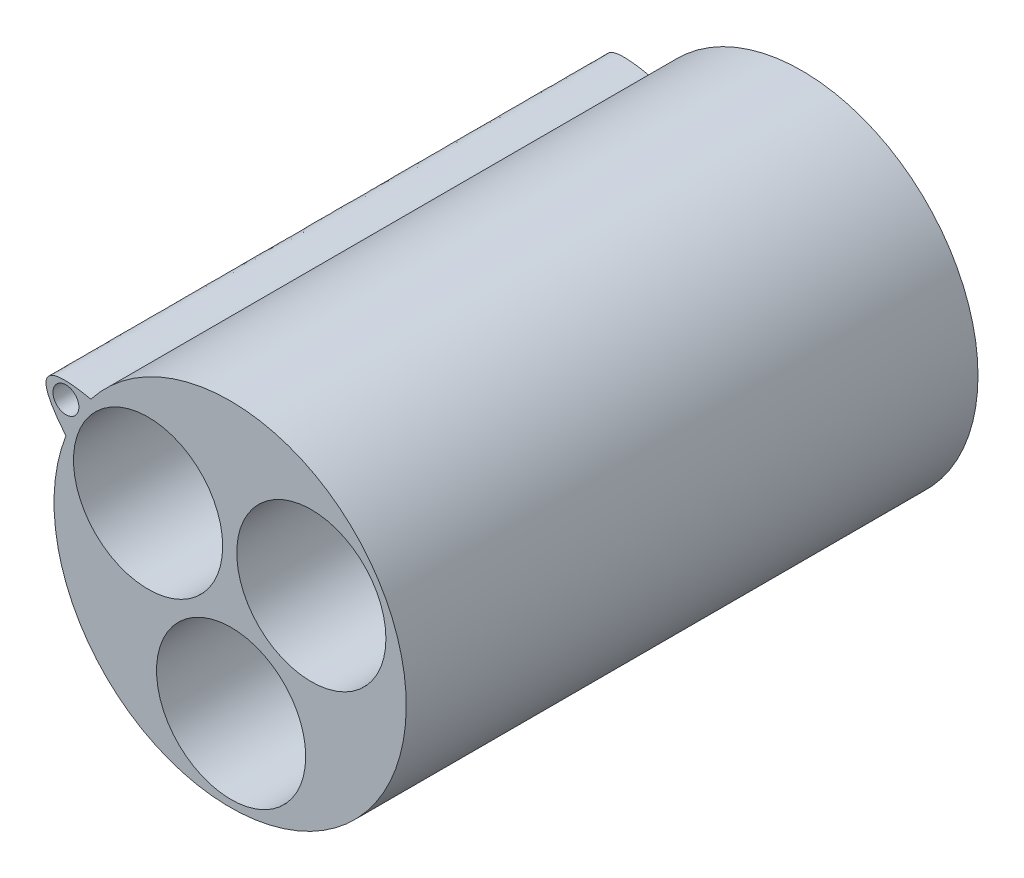
SolidWorks part; units mm, degrees
ref_plane "Front Plane" through (0, 0, 0) normal (0, 0, 1) x (1, 0, 0)
ref_plane "Top Plane" through (0, 0, 0) normal (0, 1, 0) x (1, 0, 0)
ref_plane "Right Plane" through (0, 0, 0) normal (1, 0, 0) x (0, 0, -1)
sketch "Sketch1" plane through (0, 0, 0) normal (0, 0, 1) x (1, 0, 0)
  line L0 (0, 0) -> (-20.1218, 11.3741) construction
  line L1 (0, 0) -> (19.9112, 11.7389) construction
  line L2 (0, 0) -> (0.2377, -23.114) construction
  circle A4 centre (0.1189, -11.557) radius 9.144
  circle A5 centre (9.9556, 5.8695) radius 9.144
  circle A6 centre (-10.0609, 5.687) radius 9.144
  circle A8 centre (0, 0) radius 21.59
  point P1 (2.188, 1.29)
  point P2 (-2.2112, 1.2499)
  point P6 (0.0261, -2.54)
  point P7 (9.9556, 5.8695)
  point P8 (-10.0609, 5.687)
  point P9 (0.1189, -11.557)
  dimension "D1" = 2.54
  dimension "D2" = 2.54
  dimension "D3" = 2.54
  dimension "D4" = 9.017
  dimension "D5" = 9.017
  dimension "D6" = 9.017
extrude "Boss-Extrude1" add sketch "Sketch1" along normal blind 70.1
sketch "Sketch2" plane through (0, 0, 70.1) normal (0, 0, 1) x (1, 0, 0)
  line L0 (0, 0) -> (0, 20.7928) construction
  line L1 (0, 0) -> (29.3992, -16.9737) construction
  line L2 (0, 0) -> (-30.647, -17.6941)
  line L3 (0, 0) -> (-40.2688, 23.2492) construction
  circle A1 centre (-20.1344, 11.6246) radius 1.5875
  circle A2 centre (0, 0) radius 21.59
  spline S0 degree 2 poles (-20.1344, 7.7932) (-26.2443, 15.2034) (-17.0754, 13.2121) knots 0 0 0 1 1 1
  point P3 (-20.1823, 11.6522)
  point P9 (-22.382, 12.9222)
  point P11 (-20.1344, 7.7932)
  point P12 (-17.0754, 13.2121)
  dimension "D4" = 23.3045
  dimension "D5" = 2.54
  dimension "D1" = 120
  dimension "D2" = 120
  dimension "D3" = 60
extrude "Boss-Extrude3" add sketch "Sketch2" against normal blind 68.58 contours S0 A2 A1
